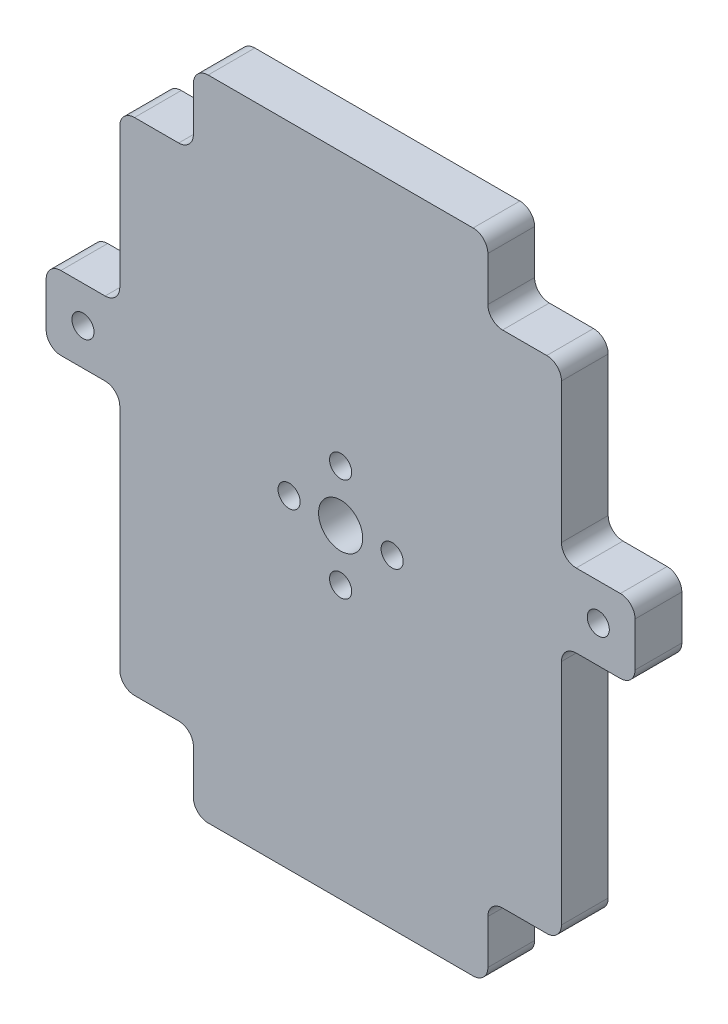
SolidWorks part; units mm, degrees
ref_plane "Front" through (0, 0, 0) normal (0, 0, 1) x (1, 0, 0)
ref_plane "Top" through (0, 0, 0) normal (0, 1, 0) x (1, 0, 0)
ref_plane "Right" through (0, 0, 0) normal (1, 0, 0) x (0, 0, -1)
sketch "草图1" plane through (0, 0, 0) normal (0, 0, 1) x (1, 0, 0)
  line L0 (-28.0368, 40.4832) -> (-28.0368, 21.4832)
  line L1 (-26.0368, -25.5168) -> (-20.0368, -25.5168)
  line L2 (-18.0368, -27.5168) -> (-18.0368, -33.5168)
  line L3 (-16.0368, -35.5168) -> (19.9632, -35.5168)
  line L4 (21.9632, -33.5168) -> (21.9632, -27.5168)
  line L5 (23.9632, -25.5168) -> (29.9632, -25.5168)
  line L6 (31.9632, -23.5168) -> (31.9632, 7.4832)
  line L7 (33.9632, 9.4832) -> (39.9632, 9.4832)
  line L8 (41.9632, 11.4832) -> (41.9632, 17.4832)
  line L9 (39.9632, 19.4832) -> (33.9632, 19.4832)
  line L10 (31.9632, 21.4832) -> (31.9632, 40.4832)
  line L11 (29.9632, 42.4832) -> (23.9632, 42.4832)
  line L12 (21.9632, 44.4832) -> (21.9632, 50.4832)
  line L13 (19.9632, 52.4832) -> (-16.0368, 52.4832)
  line L14 (-18.0368, 50.4832) -> (-18.0368, 44.4832)
  line L15 (-20.0368, 42.4832) -> (-26.0368, 42.4832)
  line L16 (-30.0368, 19.4832) -> (-36.0368, 19.4832)
  line L17 (-38.0368, 17.4832) -> (-38.0368, 11.4832)
  line L18 (-36.0368, 9.4832) -> (-30.0368, 9.4832)
  line L19 (-28.0368, 7.4832) -> (-28.0368, -23.5168)
  arc A0 (31.9632, -23.5168) -> (29.9632, -25.5168) centre (29.9632, -23.5168) cw
  arc A1 (23.9632, -25.5168) -> (21.9632, -27.5168) centre (23.9632, -27.5168) ccw
  arc A2 (21.9632, -33.5168) -> (19.9632, -35.5168) centre (19.9632, -33.5168) cw
  arc A3 (-16.0368, -35.5168) -> (-18.0368, -33.5168) centre (-16.0368, -33.5168) cw
  arc A4 (-18.0368, -27.5168) -> (-20.0368, -25.5168) centre (-20.0368, -27.5168) ccw
  arc A5 (-26.0368, -25.5168) -> (-28.0368, -23.5168) centre (-26.0368, -23.5168) cw
  arc A6 (-28.0368, 7.4832) -> (-30.0368, 9.4832) centre (-30.0368, 7.4832) ccw
  arc A7 (-36.0368, 9.4832) -> (-38.0368, 11.4832) centre (-36.0368, 11.4832) cw
  arc A8 (-36.0368, 19.4832) -> (-38.0368, 17.4832) centre (-36.0368, 17.4832) ccw
  arc A9 (-30.0368, 19.4832) -> (-28.0368, 21.4832) centre (-30.0368, 21.4832) ccw
  arc A10 (-26.0368, 42.4832) -> (-28.0368, 40.4832) centre (-26.0368, 40.4832) ccw
  arc A11 (33.9632, 9.4832) -> (31.9632, 7.4832) centre (33.9632, 7.4832) ccw
  arc A12 (41.9632, 11.4832) -> (39.9632, 9.4832) centre (39.9632, 11.4832) cw
  arc A13 (41.9632, 17.4832) -> (39.9632, 19.4832) centre (39.9632, 17.4832) ccw
  arc A14 (33.9632, 19.4832) -> (31.9632, 21.4832) centre (33.9632, 21.4832) cw
  arc A15 (31.9632, 40.4832) -> (29.9632, 42.4832) centre (29.9632, 40.4832) ccw
  arc A16 (23.9632, 42.4832) -> (21.9632, 44.4832) centre (23.9632, 44.4832) cw
  arc A17 (21.9632, 50.4832) -> (19.9632, 52.4832) centre (19.9632, 50.4832) ccw
  arc A18 (-18.0368, 50.4832) -> (-16.0368, 52.4832) centre (-16.0368, 50.4832) cw
  arc A19 (-18.0368, 44.4832) -> (-20.0368, 42.4832) centre (-20.0368, 44.4832) cw
  point P22 (31.9632, -25.5168)
  point P25 (21.9632, -25.5168)
  point P28 (21.9632, -35.5168)
  point P31 (-18.0368, -35.5168)
  point P34 (-18.0368, -25.5168)
  point P37 (-28.0368, -25.5168)
  point P42 (-38.0368, 9.4832)
  point P45 (-38.0368, 19.4832)
  point P48 (-28.0368, 19.4832)
  point P51 (-28.0368, 42.4832)
  point P54 (31.9632, 9.4832)
  point P57 (41.9632, 9.4832)
  point P60 (41.9632, 19.4832)
  point P65 (31.9632, 42.4832)
  point P68 (21.9632, 42.4832)
  point P71 (21.9632, 52.4832)
  point P74 (-18.0368, 52.4832)
  dimension "D15" = 2
  dimension "D1" = 68
  dimension "D2" = 10
  dimension "D3" = 10
  dimension "D4" = 40
  dimension "D5" = 10
  dimension "D6" = 10
  dimension "D7" = 35
  dimension "D8" = 10
  dimension "D9" = 10
  dimension "D10" = 10
  dimension "D11" = 10
  dimension "D12" = 40
  dimension "D13" = 10
  dimension "D14" = 10
extrude "凸台-拉伸1" add sketch "草图1" along normal blind 6.35
sketch "草图2" plane through (0, 0, 6.35) normal (0, 0, 1) x (1, 0, 0)
  circle A0 centre (-33.0368, 14.4832) radius 1.5
  circle A1 centre (36.9632, 14.4832) radius 1.5
  dimension "D1" = 3
  dimension "D2" = 3
extrude "切除-拉伸1" cut sketch "草图2" against normal through all
sketch "草图3" plane through (0, 0, 6.35) normal (0, 0, 1) x (1, 0, 0)
  line L0 (-16.0368, -35.5168) -> (19.9632, -35.5168) construction
  circle A0 centre (1.9632, 8.4832) radius 3
  circle A1 centre (8.9632, 8.4832) radius 1.5
  circle A2 centre (1.9632, 15.4832) radius 1.5
  circle A3 centre (-5.0368, 8.4832) radius 1.5
  circle A4 centre (1.9632, 1.4832) radius 1.5
  dimension "D2" = 3
  dimension "D3" = 6
  dimension "D5" = 3
  dimension "D6" = 3
  dimension "D7" = 3
  dimension "D4" = 7
  dimension "D9" = 7
  dimension "D10" = 7
  dimension "D11" = 44
  dimension "D12" = 7
extrude "切除-拉伸2" cut sketch "草图3" against normal through all
